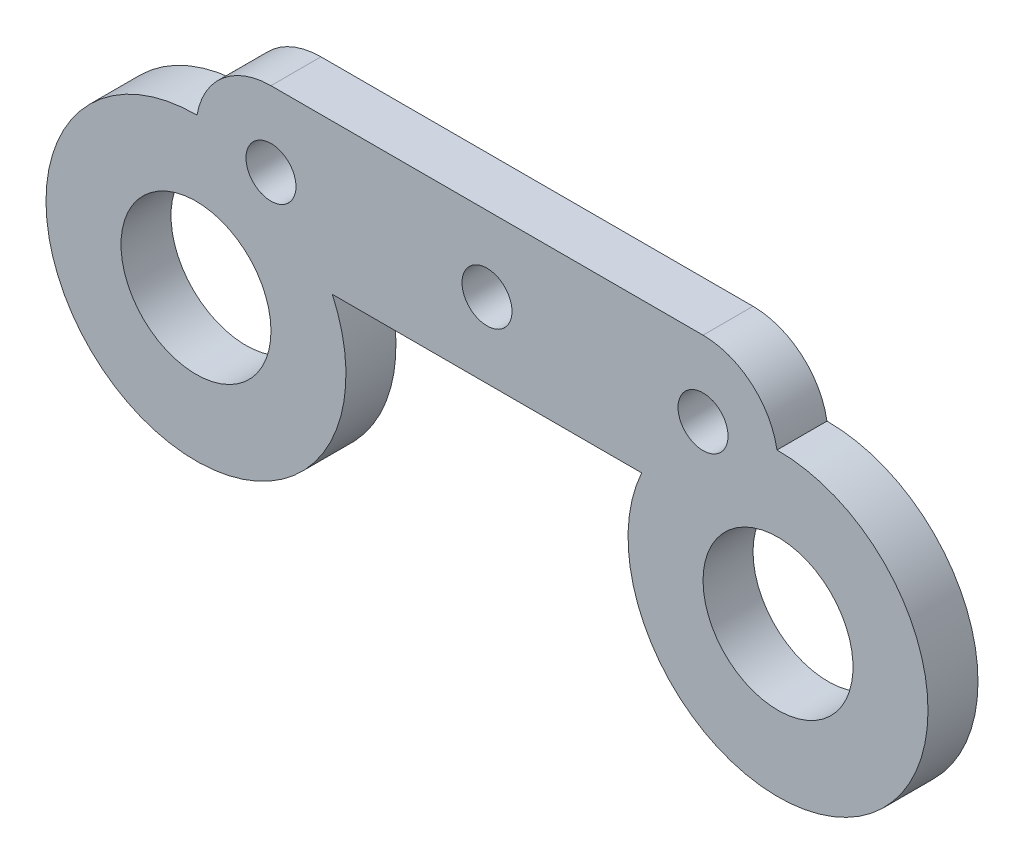
SolidWorks part; units mm, degrees
ref_plane "Front Plane" through (0, 0, 0) normal (0, 0, 1) x (1, 0, 0)
ref_plane "Top Plane" through (0, 0, 0) normal (0, 1, 0) x (1, 0, 0)
ref_plane "Right Plane" through (0, 0, 0) normal (1, 0, 0) x (0, 0, -1)
sketch "Sketch1" plane through (0, 0, 0) normal (0, 0, 1) x (1, 0, 0)
  line L1 (-8.6421, 3) -> (8.6421, 3)
  line L3 (-6.1878, -3) -> (6.1878, -3)
  arc A0 (-11.6002, 0.4999) -> (-6.1878, -3) centre (-11.6421, -5.5) ccw
  circle A5 centre (-11.6421, -5.5) radius 3
  arc A10 (6.1878, -3) -> (11.6002, 0.4999) centre (11.6421, -5.5) ccw
  circle A12 centre (11.6421, -5.5) radius 3
  circle A13 centre (8.6421, 0) radius 1
  arc A14 (8.6421, 3) -> (11.6002, 0.4999) centre (8.6421, 0) cw
  circle A15 centre (-8.6421, 0) radius 1
  arc A16 (-8.6421, 3) -> (-11.6002, 0.4999) centre (-8.6421, 0) ccw
  circle A17 centre (0, 0) radius 1
  dimension "D2" = 2
  dimension "D3" = 6
  dimension "D4" = 6.1878
  dimension "D5" = 8.6421
  dimension "D7" = 6.1878
  dimension "D1" = 6
  dimension "D6" = 11.6002
extrude "Boss-Extrude1" add sketch "Sketch1" along normal blind 2
sketch "Sketch2" plane through (0, -3, 0) normal (0, -1, 0) x (1, 0, 0)
  line L0 (6.1878, 2) -> (6.1878, 0) construction
  line L1 (-6.1878, 0) -> (6.1878, 0) construction
  circle A0 centre (0, 1) radius 0.5
  dimension "D1" = 1
  dimension "D2" = 6.1878
  dimension "D3" = 1
extrude "Cut-Extrude1" cut sketch "Sketch2" against normal blind 0.5
